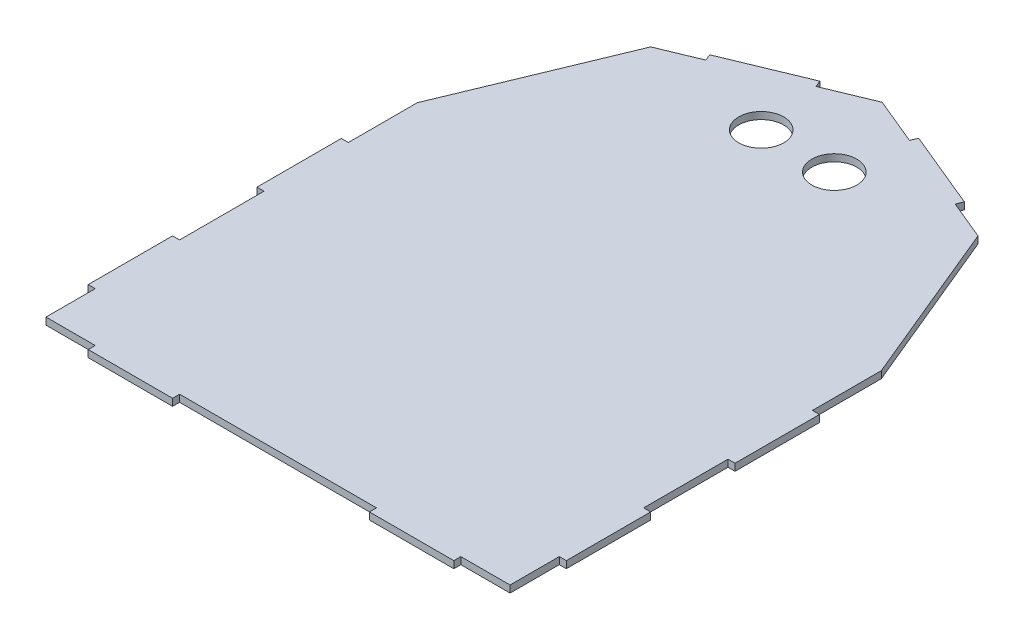
SolidWorks part; units mm, degrees
ref_plane "Front Plane" through (0, 0, 0) normal (0, 0, 1) x (1, 0, 0)
ref_plane "Top Plane" through (0, 0, 0) normal (0, 1, 0) x (1, 0, 0)
ref_plane "Right Plane" through (0, 0, 0) normal (1, 0, 0) x (0, 0, -1)
sketch "Sketch2" plane through (0, 0, 0) normal (0, 1, 0) x (1, 0, 0)
  line L0 (0, 0) -> (170, 0)
  line L1 (0, 0) -> (0, 135)
  line L2 (0, 135) -> (170, 135) construction
  line L3 (170, 0) -> (170, 135)
  line L13 (170, 135) -> (145.1041, 195.1041)
  line L14 (145.1041, 195.1041) -> (85, 220)
  line L15 (85, 220) -> (24.8959, 195.1041)
  line L16 (24.8959, 195.1041) -> (0, 135)
  line L17 (0, 135) -> (24.8959, 74.8959) [skipped]
  line L18 (24.8959, 74.8959) -> (85, 50) [skipped]
  line L19 (85, 50) -> (145.1041, 74.8959) [skipped]
  line L20 (145.1041, 74.8959) -> (170, 135) [skipped]
  arc A0 (170, 135) -> (0, 135) centre (85, 135) ccw construction
  circle A2 centre (85, 135) radius 78.5298 construction
  point P5 (85, 220)
  dimension "D3" = 157.0595
  dimension "D1" = 170
  dimension "D2" = 220
extrude "Boss-Extrude1" add sketch "Sketch2" along normal blind 2.5
sketch "Sketch6" plane through (0, 2.5, 0) normal (0, 1, 0) x (1, 0, 0)
  line L0 (85, 220) -> (85, 0) construction
  line L1 (0, 0) -> (170, 0) construction
  line L2 (170, 0) -> (170, 135) construction
  line L3 (145.1041, 195.1041) -> (85, 220) construction
  line L4 (170, 135) -> (145.1041, 195.1041) construction
  line L5 (50, 0) -> (120, 0)
  line L6 (170, 0) -> (170, 20)
  line L7 (145.1041, 195.1041) -> (130.2892, 201.2406)
  line L8 (170, 135) -> (145.1041, 195.1041)
  line L9 (50, 2.5) -> (120, 2.5)
  line L10 (167.5, 2.5) -> (167.5, 20)
  line L11 (167.5, 134.5027) -> (143.1907, 193.1907)
  line L12 (143.1907, 193.1907) -> (129.3325, 198.9309)
  line L13 (120, 2.5) -> (120, 0)
  line L14 (143.1907, 193.1907) -> (84.0433, 217.6903) construction
  line L15 (150, 2.5) -> (150, 0)
  line L16 (167.5, 20) -> (170, 20)
  line L17 (167.5, 50) -> (170, 50)
  line L18 (167.5, 80) -> (170, 80)
  line L19 (167.5, 110) -> (170, 110)
  line L20 (101.6161, 210.4114) -> (102.5728, 212.7211)
  line L21 (129.3325, 198.9309) -> (130.2892, 201.2406)
  line L22 (101.6161, 210.4114) -> (85, 217.294)
  line L23 (102.5728, 212.7211) -> (85, 220)
  line L24 (150, 2.5) -> (167.5, 2.5)
  line L25 (145.1041, 195.1041) -> (85, 220) construction
  line L26 (150, 0) -> (170, 0)
  line L27 (85, 2.5) -> (167.5, 2.5) construction
  line L28 (167.5, 50) -> (167.5, 80)
  line L29 (85, 0) -> (170, 0) construction
  line L30 (170, 50) -> (170, 80)
  line L31 (167.5, 2.5) -> (167.5, 134.5027) construction
  line L32 (167.5, 110) -> (167.5, 134.5027)
  line L33 (170, 0) -> (170, 135) construction
  line L34 (170, 110) -> (170, 135)
  line L35 (0, 110) -> (0, 135)
  line L36 (2.5, 110) -> (2.5, 134.5027)
  line L37 (0, 50) -> (0, 80)
  line L38 (2.5, 50) -> (2.5, 80)
  line L39 (20, 0) -> (0, 0)
  line L40 (20, 2.5) -> (2.5, 2.5)
  line L41 (67.4272, 212.7211) -> (85, 220)
  line L42 (68.3839, 210.4114) -> (85, 217.294)
  line L43 (40.6675, 198.9309) -> (39.7108, 201.2406)
  line L44 (68.3839, 210.4114) -> (67.4272, 212.7211)
  line L45 (2.5, 110) -> (0, 110)
  line L46 (2.5, 80) -> (0, 80)
  line L47 (2.5, 50) -> (0, 50)
  line L48 (2.5, 20) -> (0, 20)
  line L49 (20, 2.5) -> (20, 0)
  line L50 (50, 2.5) -> (50, 0)
  line L51 (26.8093, 193.1907) -> (40.6675, 198.9309)
  line L52 (2.5, 134.5027) -> (26.8093, 193.1907)
  line L53 (2.5, 2.5) -> (2.5, 20)
  line L54 (0, 135) -> (24.8959, 195.1041)
  line L55 (24.8959, 195.1041) -> (39.7108, 201.2406)
  line L56 (0, 0) -> (0, 20)
  dimension "D2" = 30
  dimension "D3" = 15
  dimension "D4" = 30
  dimension "D5" = 80
  dimension "D6" = 30
  dimension "D7" = 20
  dimension "D8" = 30
  dimension "D9" = 20
  dimension "D1" = 2.5
extrude "Cut-Extrude3" cut sketch "Sketch6" against normal through all
sketch "Sketch7" plane through (0, 2.5, 0) normal (0, 1, 0) x (1, 0, 0)
  line L0 (85, 217.294) -> (85, 2.5) construction
  line L1 (120, 2.5) -> (50, 2.5) construction
  circle A0 centre (72, 187.294) radius 8
  circle A1 centre (98, 187.294) radius 8
  dimension "D1" = 16
  dimension "D2" = 30
  dimension "D3" = 13
  dimension "D4" = 13
extrude "Cut-Extrude4" cut sketch "Sketch7" against normal through all
